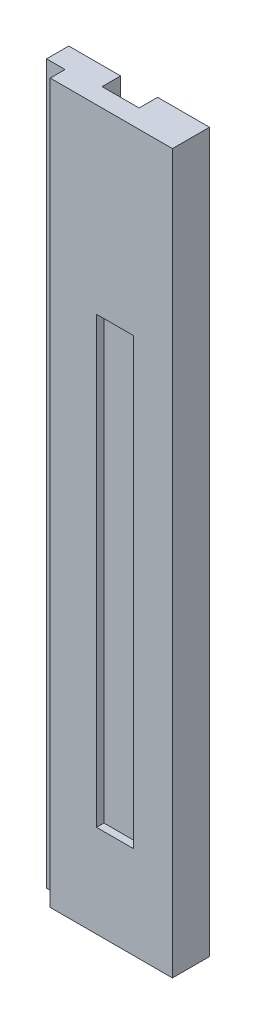
SolidWorks part; units mm, degrees
other "Markup1"
sketch "Sketch25" plane through (2, 18.9717, -1) normal (0.6328, -0.4558, -0.626) x (-0.6565, -0.7445, -0.1216)
material "ABS"
ref_plane "Alzado" through (0, 0, 0) normal (0, 0, 1) x (1, 0, 0)
ref_plane "Planta" through (0, 0, 0) normal (0, 1, 0) x (1, 0, 0)
ref_plane "Vista lateral" through (0, 0, 0) normal (1, 0, 0) x (0, 0, -1)
sketch "Sketch1" plane through (0, 0, 0) normal (0, 0, 1) x (1, 0, 0)
  line L1 (-14, 88.9717) -> (0, 88.9717)
  line L2 (-14, 88.9717) -> (-14, -11.0283)
  line L3 (-14, -11.0283) -> (0, -11.0283)
  line L4 (0, 88.9717) -> (0, -11.0283)
  line L5 (-14, 88.9717) -> (0, -11.0283) construction
  line L6 (-14, -11.0283) -> (0, 88.9717) construction
  point P0 (-7, 38.9717)
  dimension "D1" = 14
  dimension "D2" = 100
extrude "Boss-Extrude1" add sketch "Sketch1" along normal blind 2
sketch "Sketch2" plane through (0, 0, 2) normal (0, 0, 1) x (1, 0, 0)
  line L0 (-14, -11.0283) -> (0, -11.0283) construction
  line L1 (-14, 88.9717) -> (-12, 88.9717)
  line L2 (-14, 88.9717) -> (-14, -11.0283)
  line L3 (-14, -11.0283) -> (-12, -11.0283)
  line L4 (-12, 88.9717) -> (-12, -11.0283)
  line L5 (0, 88.9717) -> (-14, 88.9717) construction
  line L6 (0, -11.0283) -> (-2, -11.0283)
  line L7 (0, -11.0283) -> (0, 88.9717)
  line L8 (0, 88.9717) -> (-2, 88.9717)
  line L9 (-2, -11.0283) -> (-2, 88.9717)
  dimension "D1" = 2
  dimension "D2" = 2
extrude "Boss-Extrude2" add sketch "Sketch2" along normal blind 4
sketch "Sketch3" plane through (0, 0, 0) normal (1, 0, 0) x (0, 0, -1)
  line L1 (0, 88.9717) -> (-2, 88.9717)
  line L2 (0, 88.9717) -> (0, -11.0283)
  line L3 (0, -11.0283) -> (-2, -11.0283)
  line L4 (-2, 88.9717) -> (-2, -11.0283)
extrude "Boss-Extrude4" add sketch "Sketch3" along normal blind 2
sketch "Sketch4" plane through (-14, 0, 0) normal (-1, 0, 0) x (0, 0, 1)
  line L1 (0, 88.9717) -> (2, 88.9717)
  line L2 (0, 88.9717) -> (0, -11.0283)
  line L3 (0, -11.0283) -> (2, -11.0283)
  line L4 (2, 88.9717) -> (2, -11.0283)
extrude "Boss-Extrude5" add sketch "Sketch4" along normal blind 2
sketch "Sketch6" plane through (0, 0, 0) normal (0, 0, -1) x (-1, 0, 0)
  line L1 (16, -11.0283) -> (-2, -11.0283)
  line L2 (16, -11.0283) -> (16, 88.9717)
  line L3 (16, 88.9717) -> (-2, 88.9717)
  line L4 (-2, -11.0283) -> (-2, 88.9717)
extrude "Boss-Extrude6" add sketch "Sketch6" along normal blind 1
sketch "Sketch7" plane through (0, 0, -1) normal (0, 0, -1) x (-1, 0, 0)
  line L0 (-2, -11.0283) -> (16, -11.0283) construction
  line L1 (8.5, -11.0283) -> (5.5, -11.0283)
  line L2 (8.5, -11.0283) -> (8.5, 88.9717)
  line L3 (8.5, 88.9717) -> (5.5, 88.9717)
  line L4 (5.5, -11.0283) -> (5.5, 88.9717)
  line L5 (16, 88.9717) -> (-2, 88.9717) construction
  dimension "D1" = 3
  dimension "D2" = 7.5
extrude "Cut-Extrude1" cut sketch "Sketch7" against normal blind 1
sketch "Sketch8" plane through (0, 88.9717, 0) normal (0, 1, 0) x (1, 0, 0)
  line L0 (-2, -2) -> (-2, 1) construction
  line L1 (-5.5, 1) -> (2, 1) construction
  line L2 (2, 1) -> (-5.5, 1)
  line L12 (-5.5, 1) -> (-5.5, 0)
  line L13 (-5.5, 0) -> (-8.5, 0) construction
  line L14 (-5.5, 0) -> (-5.5, 1) construction
  line L15 (-5.5, 0) -> (-8.5, 0)
  line L16 (-8.5, 0) -> (-8.5, 1)
  line L17 (-8.5, 1) -> (-16, 1)
  line L18 (-16, 1) -> (-16, -2)
  line L19 (-16, -2) -> (-14, -2)
  line L20 (-14, -2) -> (-14, -6)
  line L21 (-14, -6) -> (-14, -2) construction
  line L22 (-14, -6) -> (-12, -6)
  line L23 (-12, -6) -> (-12, -2)
  line L24 (-12, -2) -> (-2, -2) construction
  line L25 (-12, -6) -> (-12, -2) construction
  line L26 (-12, -2) -> (-2, -2)
  line L27 (-2, -2) -> (-2, -6)
  line L28 (-2, -6) -> (0, -6)
  line L29 (0, -6) -> (0, -2)
  line L30 (0, -2) -> (2, -2)
  line L31 (2, -2) -> (2, 1)
extrude "Boss-Extrude7" add sketch "Sketch8" along normal blind 50
sketch "Sketch9" plane through (0, 138.9717, 0) normal (0, 1, 0) x (1, 0, 0)
  line L0 (-8.5, 1) -> (-16, 1) construction
  line L1 (-8.5, 1) -> (-11.5, 1)
  line L2 (-8.5, 1) -> (-8.5, 0)
  line L3 (-8.5, 0) -> (-11.5, 0)
  line L4 (-11.5, 1) -> (-11.5, 0)
  line L5 (-12, -2) -> (-12, 1) construction
  dimension "D1" = 3
  dimension "D2" = 1
  dimension "D3" = 0
extrude "Cut-Extrude2" cut sketch "Sketch9" against normal blind 150
sketch "Sketch10" plane through (0, 138.9717, 0) normal (0, 1, 0) x (1, 0, 0)
  line L0 (-5.5, 0) -> (-11.5, 0) construction
  line L1 (-5.5, 1) -> (-8.5, 1)
  line L2 (-5.5, 1) -> (-5.5, 0)
  line L3 (-5.5, 0) -> (-8.5, 0)
  line L4 (-8.5, 1) -> (-8.5, 0)
extrude "Boss-Extrude8" add sketch "Sketch10" against normal blind 150
sketch "Sketch11" plane through (0, 0, 2) normal (0, 0, 1) x (1, 0, 0)
  line L0 (-14, -11.0283) -> (-14, 138.9717) construction
  line L1 (-16, -11.0283) -> (-14, -11.0283)
  line L2 (-16, -11.0283) -> (-16, 38.9717)
  line L3 (-16, 38.9717) -> (-14, 38.9717)
  line L4 (-14, -11.0283) -> (-14, 38.9717)
  dimension "D1" = 50
extrude "Cut-Extrude3" cut sketch "Sketch11" against normal blind 50
sketch "Sketch14" plane through (0, 0, 6) normal (0, 0, 1) x (1, 0, 0)
  line L0 (2, 138.9717) -> (2, -11.0283) construction
  line L1 (-14, -11.0283) -> (2, -11.0283)
  line L2 (-14, -11.0283) -> (-14, 18.9717)
  line L3 (-14, 18.9717) -> (2, 18.9717)
  line L4 (2, -11.0283) -> (2, 18.9717)
  dimension "D1" = 30
extrude "Cut-Extrude4" cut sketch "Sketch14" against normal blind 50
sketch "Sketch15" plane through (0, 0, 2) normal (0, 0, 1) x (1, 0, 0)
  line L0 (-2, 138.9717) -> (-2, 18.9717) construction
  line L1 (-12, 138.9717) -> (-2, 138.9717)
  line L2 (-12, 138.9717) -> (-12, 136.9717)
  line L3 (-12, 136.9717) -> (-2, 136.9717)
  line L4 (-2, 138.9717) -> (-2, 136.9717)
  dimension "D1" = 2
extrude "Boss-Extrude9" add sketch "Sketch15" along normal blind 4
sketch "Sketch16" plane through (0, 0, 2) normal (0, 0, 1) x (1, 0, 0)
  line L0 (-2, 136.9717) -> (-2, 18.9717) construction
  line L1 (-12, 136.9717) -> (-2, 136.9717)
  line L2 (-12, 136.9717) -> (-12, 128.9717)
  line L3 (-12, 128.9717) -> (-2, 128.9717)
  line L4 (-2, 136.9717) -> (-2, 128.9717)
  dimension "D1" = 8
extrude "Boss-Extrude10" add sketch "Sketch16" along normal blind 4
sketch "Sketch21" plane through (0, 0, 6) normal (0, 0, 1) x (1, 0, 0)
  line L1 (-12, 128.9717) -> (-2, 128.9717)
  line L2 (-12, 128.9717) -> (-12, 136.9717)
  line L3 (-12, 136.9717) -> (-2, 136.9717)
  line L4 (-2, 128.9717) -> (-2, 136.9717)
  dimension "D1" = 8
extrude "Cut-Extrude5" cut sketch "Sketch21" against normal blind 4
sketch "Sketch23" plane through (0, 0, 6) normal (0, 0, 1) x (1, 0, 0)
  line L1 (2, 138.9717) -> (-14, 138.9717)
  line L2 (2, 138.9717) -> (2, 18.9717)
  line L3 (2, 18.9717) -> (-14, 18.9717)
  line L4 (-14, 138.9717) -> (-14, 18.9717)
extrude "Cut-Extrude7" cut sketch "Sketch23" against normal blind 2
sketch "Sketch24" plane through (0, 0, 0) normal (0, 0, -1) x (-1, 0, 0)
  line L0 (11.5, 18.9717) -> (11.5, 138.9717) construction
  line L1 (8.5, 138.9717) -> (11.5, 138.9717)
  line L2 (8.5, 138.9717) -> (8.5, 98.9717)
  line L3 (8.5, 98.9717) -> (11.5, 98.9717)
  line L4 (11.5, 138.9717) -> (11.5, 98.9717)
  dimension "D1" = 40
extrude "Boss-Extrude13" add sketch "Sketch24" along normal blind 1
sketch "Sketch26" plane through (0, 18.9717, 0) normal (0, -1, 0) x (1, 0, 0)
  line L0 (-14, 4) -> (-12, 4)
  line L1 (-12, 4) -> (-12, 2)
  line L2 (-12, 2) -> (-2, 2)
  line L3 (-2, 2) -> (-2, 4)
  line L4 (-2, 4) -> (0, 4)
  line L5 (0, 4) -> (0, 2)
  line L6 (0, 2) -> (2, 2)
  line L7 (2, 2) -> (2, -1)
  line L8 (2, -1) -> (-8.5, -1)
  line L9 (-8.5, -1) -> (-8.5, 0)
  line L10 (-8.5, 0) -> (-11.5, 0)
  line L11 (-11.5, 0) -> (-11.5, -1)
  line L12 (-11.5, 0) -> (-11.5, -1) construction
  line L13 (-11.5, -1) -> (-11.5, 0) construction
  line L14 (-11.5, -1) -> (-14, -1)
  line L15 (-14, -1) -> (-14, 4)
extrude "Boss-Extrude14" add sketch "Sketch26" along normal blind 50
sketch "Sketch27" plane through (0, 0, 0) normal (1, 0, 0) x (0, 0, -1)
  line L1 (-4, 138.9717) -> (-2, 138.9717)
  line L2 (-4, 138.9717) -> (-4, -31.0283)
  line L3 (-4, -31.0283) -> (-2, -31.0283)
  line L4 (-2, 138.9717) -> (-2, -31.0283)
extrude "Boss-Extrude15" add sketch "Sketch27" along normal through all
sketch "Sketch28" plane through (2, 0, 0) normal (1, 0, 0) x (0, 0, -1)
  line L1 (-4, 138.9717) -> (1, 138.9717)
  line L2 (-4, 138.9717) -> (-4, -31.0283)
  line L3 (-4, -31.0283) -> (1, -31.0283)
  line L4 (1, 138.9717) -> (1, -31.0283)
extrude "Boss-Extrude16" add sketch "Sketch28" along normal blind 18
sketch "Sketch29" plane through (20, 0, 0) normal (1, 0, 0) x (0, 0, -1)
  line L1 (-4, 138.9717) -> (1, 138.9717)
  line L2 (-4, 138.9717) -> (-4, -31.0283)
  line L3 (-4, -31.0283) -> (1, -31.0283)
  line L4 (1, 138.9717) -> (1, -31.0283)
extrude "Boss-Extrude17" add sketch "Sketch29" against normal blind 40
sketch "Sketch30" plane through (-20, 0, 0) normal (-1, 0, 0) x (0, 0, 1)
  line L0 (-1, 138.9717) -> (4, 138.9717) construction
  line L1 (4, -31.0283) -> (3, -31.0283)
  line L2 (4, -31.0283) -> (4, 138.9717)
  line L3 (4, 138.9717) -> (3, 138.9717)
  line L4 (3, -31.0283) -> (3, 138.9717)
  dimension "D1" = 1
extrude "Boss-Extrude18" add sketch "Sketch30" along normal blind 1
sketch "Sketch31" plane through (20, 0, 0) normal (1, 0, 0) x (0, 0, -1)
  line L0 (1, 138.9717) -> (-4, 138.9717) construction
  line L1 (-4, -31.0283) -> (-3, -31.0283)
  line L2 (-4, -31.0283) -> (-4, 138.9717)
  line L3 (-4, 138.9717) -> (-3, 138.9717)
  line L4 (-3, -31.0283) -> (-3, 138.9717)
  dimension "D1" = 1
extrude "Boss-Extrude19" add sketch "Sketch31" along normal blind 1
sketch "Sketch32" plane through (0, 0, -1) normal (0, 0, -1) x (-1, 0, 0)
  line L0 (20, -31.0283) -> (5, -31.0283) construction
  line L1 (20, -31.0283) -> (-20, -31.0283) construction
  line L2 (-20, 138.9717) -> (20, 138.9717) construction
  line L3 (5, -31.0283) -> (-5, -31.0283)
  line L4 (5, -31.0283) -> (5, 138.9717)
  line L5 (5, 138.9717) -> (-5, 138.9717)
  line L6 (-5, -31.0283) -> (-5, 138.9717)
  dimension "D1" = 15
  dimension "D2" = 10
extrude "Cut-Extrude8" cut sketch "Sketch32" against normal blind 2
sketch "Sketch33" plane through (0, 138.9717, 0) normal (0, 1, 0) x (1, 0, 0)
  line L1 (-20, 1) -> (20, 1)
  line L2 (-20, 1) -> (-20, -3)
  line L3 (-20, -3) -> (20, -3)
  line L4 (20, 1) -> (20, -3)
extrude "Boss-Extrude20" add sketch "Sketch33" against normal blind 1
sketch "Sketch34" plane through (0, 0, 1) normal (0, 0, -1) x (-1, 0, 0)
  line L0 (-5, 137.9717) -> (-5, -31.0283) construction
  line L1 (5, -31.0283) -> (-5, -31.0283)
  line L2 (5, -31.0283) -> (5, 8.9717)
  line L3 (5, 8.9717) -> (-5, 8.9717)
  line L4 (-5, -31.0283) -> (-5, 8.9717)
  dimension "D1" = 40
extrude "Boss-Extrude21" add sketch "Sketch34" along normal through all
sketch "Sketch35" plane through (0, 0, 4) normal (0, 0, 1) x (1, 0, 0)
  line L0 (-21, -31.0283) -> (-20, -31.0283) construction
  line L1 (21, -31.0283) -> (-21, -31.0283) construction
  line L2 (21, 138.9717) -> (-21, 138.9717) construction
  line L3 (-19.5, -31.0283) -> (-16.5, -31.0283)
  line L4 (-19.5, -31.0283) -> (-19.5, 138.9717)
  line L5 (-19.5, 138.9717) -> (-16.5, 138.9717)
  line L6 (-16.5, -31.0283) -> (-16.5, 138.9717)
  dimension "D1" = 1
  dimension "D2" = 3
  dimension "D3" = 0.5
extrude "Cut-Extrude9" cut sketch "Sketch35" against normal blind 1
sketch "Sketch36" plane through (-20, 0, 0) normal (-1, 0, 0) x (0, 0, 1)
  line L0 (-1, 138.9717) -> (3, 138.9717) construction
  line L1 (-1, -31.0283) -> (0, -31.0283)
  line L2 (-1, -31.0283) -> (-1, 138.9717)
  line L3 (-1, 138.9717) -> (0, 138.9717)
  line L4 (0, -31.0283) -> (0, 138.9717)
  dimension "D1" = 1
extrude "Boss-Extrude22" add sketch "Sketch36" along normal blind 1
sketch "Sketch37" plane through (0, 0, 3) normal (0, 0, -1) x (-1, 0, 0)
  line L1 (20, -31.0283) -> (21, -31.0283)
  line L2 (20, -31.0283) -> (20, 138.9717)
  line L3 (20, 138.9717) -> (21, 138.9717)
  line L4 (21, -31.0283) -> (21, 138.9717)
extrude "Cut-Extrude10" cut sketch "Sketch37" against normal through all
sketch "Sketch39" plane through (0, 0, 4) normal (0, 0, 1) x (1, 0, 0)
  line L0 (21, 138.9717) -> (-16.5, 138.9717) construction
  line L1 (-20, -31.0283) -> (-14, -31.0283)
  line L2 (-20, -31.0283) -> (-20, 138.9717)
  line L3 (-20, 138.9717) -> (-14, 138.9717)
  line L4 (-14, -31.0283) -> (-14, 138.9717)
  dimension "D1" = 6
extrude "Cut-Extrude11" cut sketch "Sketch39" against normal blind 4 contours L2 L1 L4 L3
sketch "Sketch40" plane through (0, 0, 1) normal (0, 0, -1) x (-1, 0, 0)
  line L1 (-5, 137.9717) -> (5, 137.9717)
  line L2 (-5, 137.9717) -> (-5, 8.9717)
  line L3 (-5, 8.9717) -> (5, 8.9717)
  line L4 (5, 137.9717) -> (5, 8.9717)
extrude "Boss-Extrude23" add sketch "Sketch40" along normal through all
sketch "Sketch41" plane through (0, 0, 4) normal (0, 0, 1) x (1, 0, 0)
  line L0 (21, 138.9717) -> (20, 138.9717) construction
  line L1 (21, 138.9717) -> (-14, 138.9717) construction
  line L2 (20, 138.9717) -> (5, 138.9717) construction
  line L3 (5, 138.9717) -> (5, 98.9717) construction
  line L5 (5, 98.9717) -> (-5, 98.9717)
  line L6 (5, 98.9717) -> (5, -21.0283)
  line L7 (5, -21.0283) -> (-5, -21.0283)
  line L8 (-5, 98.9717) -> (-5, -21.0283)
  dimension "D1" = 1
  dimension "D2" = 40
  dimension "D3" = 120
  dimension "D4" = 10
extrude "Cut-Extrude12" cut sketch "Sketch41" against normal blind 2
sketch "Sketch43" plane through (0, -31.0283, 0) normal (0, -1, 0) x (1, 0, 0)
  line L0 (-21, -1) -> (-21, 0)
  line L1 (-21, 0) -> (-14, 0)
  line L2 (-14, 0) -> (-14, 4)
  line L3 (-14, 4) -> (21, 4)
  line L4 (21, 4) -> (21, 3)
  line L5 (21, 3) -> (20, 3)
  line L6 (20, 3) -> (20, -1)
  line L7 (20, -1) -> (-21, -1)
extrude "Boss-Extrude24" add sketch "Sketch43" along normal blind 30
sketch "Sketch44" plane through (0, 138.9717, 0) normal (0, 1, 0) x (1, 0, 0)
  line L0 (-21, 1) -> (20, 1)
  line L1 (20, 1) -> (20, -3)
  line L2 (20, -3) -> (21, -3)
  line L3 (21, -3) -> (21, -4)
  line L4 (21, -4) -> (-14, -4)
  line L5 (-14, -4) -> (-14, 0)
  line L6 (-14, 0) -> (-21, 0)
  line L7 (-21, 0) -> (-21, 1)
extrude "Cut-Extrude13" cut sketch "Sketch44" against normal blind 30
sketch "Sketch45" plane through (0, 0, 4) normal (0, 0, 1) x (1, 0, 0)
  line L0 (3.5, -61.0283) -> (3.5, -38.8705) construction
  line L1 (21, -61.0283) -> (-14, -61.0283) construction
  line L2 (21, 108.9717) -> (21, 78.9717) construction
  line L3 (21, 108.9717) -> (21, -61.0283) construction
  line L4 (5, -21.0283) -> (5, 98.9717) construction
  line L5 (5, 78.9717) -> (-5, 78.9717)
  line L6 (5, 78.9717) -> (5, -41.0283)
  line L7 (5, -41.0283) -> (-5, -41.0283)
  line L8 (-5, 78.9717) -> (-5, -41.0283)
  line L9 (-5, 98.9717) -> (-5, -21.0283) construction
  line L10 (-14, 108.9717) -> (21, 108.9717) construction
  dimension "D1" = 30
  dimension "D2" = 30
  dimension "D3" = 120
extrude "Cut-Extrude14" cut sketch "Sketch45" against normal blind 2
sketch "Sketch46" plane through (0, 0, 4) normal (0, 0, 1) x (1, 0, 0)
  line L0 (5, -41.0283) -> (5, 78.9717) construction
  line L1 (5, -41.0283) -> (5, 98.9717) construction
  line L3 (5, 78.9717) -> (-5, 78.9717)
  line L4 (5, 78.9717) -> (5, 98.9717)
  line L5 (5, 98.9717) -> (-5, 98.9717)
  line L6 (-5, 78.9717) -> (-5, 98.9717)
  dimension "D1" = 120
extrude "Boss-Extrude25" add sketch "Sketch46" against normal blind 2
sketch "Sketch47" plane through (0, 0, 4) normal (0, 0, 1) x (1, 0, 0)
  line L0 (3.5, -61.0283) -> (3.5, -36.0283) construction
  line L3 (3.5, 108.9717) -> (3.5, 83.9717) construction
  line L4 (-14, 108.9717) -> (21, 108.9717) construction
  line L5 (21, -61.0283) -> (-14, -61.0283) construction
  line L6 (-5, 78.9717) -> (-5, -41.0283) construction
  line L7 (-5, -36.0283) -> (5, -36.0283)
  line L8 (-5, -36.0283) -> (-5, -41.0283)
  line L9 (-5, -41.0283) -> (5, -41.0283)
  line L10 (5, -36.0283) -> (5, -41.0283)
  dimension "D1" = 25
  dimension "D2" = 25
extrude "Boss-Extrude26" add sketch "Sketch47" against normal blind 2
sketch "Sketch48" plane through (0, 0, 4) normal (0, 0, 1) x (1, 0, 0)
  line L1 (-5, 78.9717) -> (5, 78.9717)
  line L2 (-5, 78.9717) -> (-5, 83.9717)
  line L3 (-5, 83.9717) -> (5, 83.9717)
  line L4 (5, 78.9717) -> (5, 83.9717)
  dimension "D1" = 5
extrude "Cut-Extrude15" cut sketch "Sketch48" against normal blind 2
sketch "Sketch52" plane through (0, 0, 4) normal (0, 0, 1) x (1, 0, 0)
  line L1 (-5, 83.9717) -> (5, 83.9717)
  line L2 (-5, 83.9717) -> (-5, -36.0283)
  line L3 (-5, -36.0283) -> (5, -36.0283)
  line L4 (5, 83.9717) -> (5, -36.0283)
extrude "Boss-Extrude27" add sketch "Sketch52" against normal blind 2
sketch "Sketch53" plane through (0, 0, 4) normal (0, 0, 1) x (1, 0, 0)
  line L0 (21, -61.0283) -> (-14, -61.0283) construction
  line L1 (-1.5, 83.9717) -> (8.5, 83.9717)
  line L2 (-1.5, 83.9717) -> (-1.5, -36.0283)
  line L3 (-1.5, -36.0283) -> (8.5, -36.0283)
  line L4 (8.5, 83.9717) -> (8.5, -36.0283)
  line L5 (21, 108.9717) -> (21, -61.0283) construction
  dimension "D1" = 120
  dimension "D2" = 10
  dimension "D3" = 25
  dimension "D4" = 12.5
extrude "Cut-Extrude16" cut sketch "Sketch53" against normal blind 2
sketch "Sketch54" plane through (0, 0, -1) normal (0, 0, -1) x (-1, 0, 0)
  line L0 (-20, -61.0283) -> (-5, -61.0283) construction
  line L1 (21, -61.0283) -> (-20, -61.0283) construction
  line L2 (-20, 108.9717) -> (21, 108.9717) construction
  line L3 (-20, -61.0283) -> (-5, -61.0283)
  line L4 (-20, -61.0283) -> (-20, 108.9717)
  line L5 (-20, 108.9717) -> (-5, 108.9717)
  line L6 (-5, -61.0283) -> (-5, 108.9717)
  line L7 (-5, 108.9717) -> (5, 108.9717) construction
  line L9 (5, 108.9717) -> (20, 108.9717)
  line L10 (5, 108.9717) -> (5, -61.0283)
  line L11 (5, -61.0283) -> (20, -61.0283)
  line L12 (20, 108.9717) -> (20, -61.0283)
  dimension "D1" = 15
  dimension "D2" = 10
  dimension "D3" = 15
extrude "Boss-Extrude28" add sketch "Sketch54" along normal blind 5
sketch "Sketch55" plane through (0, 0, -1) normal (0, 0, -1) x (-1, 0, 0)
  line L1 (21, 108.9717) -> (20, 108.9717)
  line L2 (21, 108.9717) -> (21, -61.0283)
  line L3 (21, -61.0283) -> (20, -61.0283)
  line L4 (20, 108.9717) -> (20, -61.0283)
extrude "Cut-Extrude17" cut sketch "Sketch55" against normal blind 1
sketch "Sketch56" plane through (0, 0, 3) normal (0, 0, -1) x (-1, 0, 0)
  line L1 (-20, -61.0283) -> (-21, -61.0283)
  line L2 (-20, -61.0283) -> (-20, 108.9717)
  line L3 (-20, 108.9717) -> (-21, 108.9717)
  line L4 (-21, -61.0283) -> (-21, 108.9717)
extrude "Cut-Extrude18" cut sketch "Sketch56" against normal blind 10
sketch "Sketch57" plane through (0, 0, 4) normal (0, 0, 1) x (1, 0, 0)
  line L0 (-14, 108.9717) -> (20, 108.9717) construction
  line L1 (20, -61.0283) -> (19, -61.0283)
  line L2 (20, -61.0283) -> (20, 108.9717)
  line L3 (20, 108.9717) -> (19, 108.9717)
  line L4 (19, -61.0283) -> (19, 108.9717)
  line L5 (-14, -61.0283) -> (-20, -61.0283) construction
  line L6 (-20, 108.9717) -> (-19, 108.9717)
  line L7 (-20, 108.9717) -> (-20, -61.0283)
  line L8 (-20, -61.0283) -> (-19, -61.0283)
  line L9 (-19, 108.9717) -> (-19, -61.0283)
  dimension "D1" = 1
  dimension "D2" = 1
extrude "Cut-Extrude19" cut sketch "Sketch57" against normal through all
sketch "Sketch58" plane through (0, -61.0283, 0) normal (0, -1, 0) x (1, 0, 0)
  line L0 (-19, -6) -> (-5, -6)
  line L1 (-5, -6) -> (-5, -1)
  line L2 (-5, -1) -> (5, -1)
  line L3 (5, -1) -> (5, -6)
  line L4 (19, -6) -> (5, -6) construction
  line L5 (5, -6) -> (19, -6)
  line L6 (19, -6) -> (19, 4)
  line L7 (19, 4) -> (-14, 4)
  line L8 (-14, 4) -> (-14, 0)
  line L9 (-14, 0) -> (-19, 0)
  line L10 (-19, 0) -> (-19, -6)
extrude "Boss-Extrude29" add sketch "Sketch58" along normal blind 14
sketch "Sketch59" plane through (0, -75.0283, 0) normal (0, -1, 0) x (1, 0, 0)
  line L0 (-19, -6) -> (-19, 0)
  line L1 (-19, 0) -> (-14, 0)
  line L2 (-14, 0) -> (-14, 4)
  line L3 (-14, 4) -> (19, 4)
  line L4 (19, 4) -> (19, -6)
  line L5 (19, -6) -> (5, -6)
  line L6 (5, -6) -> (5, -1)
  line L7 (5, -1) -> (-5, -1)
  line L8 (-5, -1) -> (-5, -6)
  line L9 (-5, -6) -> (-19, -6)
extrude "Cut-Extrude20" cut sketch "Sketch59" against normal blind 14
sketch "Sketch60" plane through (0, 108.9717, 0) normal (0, 1, 0) x (1, 0, 0)
  line L0 (-19, 6) -> (-5, 6)
  line L1 (-5, 6) -> (-5, 1)
  line L2 (-5, 1) -> (5, 1)
  line L3 (5, 1) -> (5, 6)
  line L4 (5, 6) -> (19, 6)
  line L5 (19, 6) -> (19, -4)
  line L6 (19, -4) -> (-14, -4)
  line L7 (-14, -4) -> (-14, 0)
  line L8 (-14, 0) -> (-19, 0)
  line L9 (-19, 0) -> (-19, 6)
extrude "Boss-Extrude30" add sketch "Sketch60" along normal blind 14
sketch "Sketch61" plane through (0, 122.9717, 0) normal (0, 1, 0) x (1, 0, 0)
  line L0 (-19, 6) -> (-5, 6)
  line L1 (-5, 6) -> (-5, 1)
  line L2 (-5, 1) -> (5, 1)
  line L3 (5, 1) -> (5, 6)
  line L4 (5, 6) -> (19, 6)
  line L5 (19, 6) -> (19, -4)
  line L6 (19, -4) -> (-14, -4)
  line L7 (-14, -4) -> (-14, 0)
  line L8 (-14, 0) -> (-19, 0)
  line L9 (-19, 0) -> (-19, 6)
extrude "Boss-Extrude31" add sketch "Sketch61" along normal blind 10
